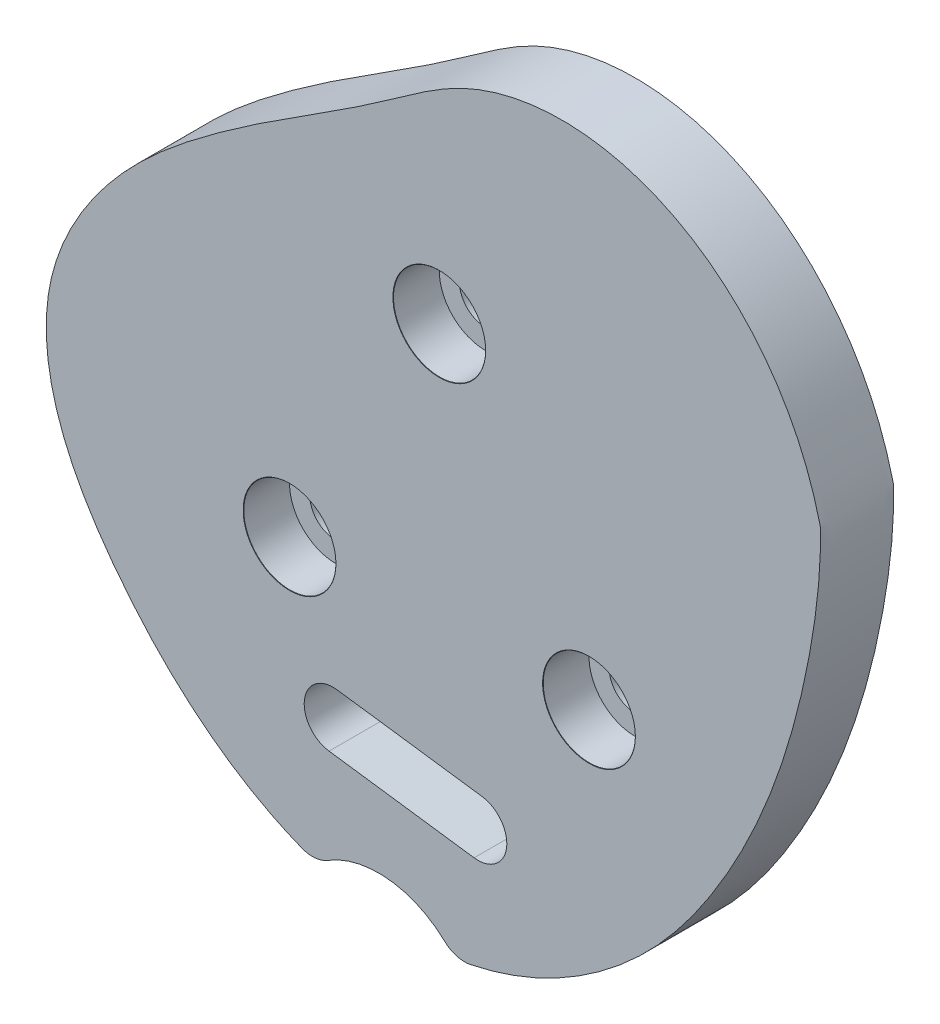
SolidWorks part; units mm, degrees
ref_plane "Front Plane" through (0, 0, 0) normal (0, 0, 1) x (1, 0, 0)
ref_plane "Top Plane" through (0, 0, 0) normal (0, 1, 0) x (1, 0, 0)
ref_plane "Right Plane" through (0, 0, 0) normal (1, 0, 0) x (0, 0, -1)
curve "Curve1"
sketch "Sketch1" plane through (0, 0, 0) normal (0, 0, 1) x (1, 0, 0)
  spline S0 degree 3 poles (20.4719, -0.3582) (20.4906, 0.0056) (20.3791, 0.3547) (20.2968, 0.7085) (20.2014, 1.0583) (20.1045, 1.4055) (20.003, 1.7496) (19.8979, 2.091) (19.7889, 2.4294) (19.6761, 2.7649) (19.5596, 3.0976) (19.4394, 3.4274) (19.3156, 3.7542) (19.1882, 4.0783) (19.0573, 4.3994) (18.9228, 4.7177) (18.7848, 5.0331) (18.6433, 5.3456) (18.4984, 5.6553) (18.3501, 5.962) (18.1985, 6.266) (18.0434, 6.567) (17.8851, 6.8652) (17.7235, 7.1605) (17.5586, 7.4529) (17.3904, 7.7425) (17.219, 8.0291) (17.0444, 8.3129) (16.8666, 8.5937) (16.6856, 8.8717) (16.5014, 9.1467) (16.3141, 9.4188) (16.1237, 9.6879) (15.9302, 9.9541) (15.7336, 10.2173) (15.5338, 10.4776) (15.3311, 10.7348) (15.1252, 10.989) (14.9164, 11.2402) (14.7045, 11.4883) (14.4895, 11.7333) (14.2716, 11.9752) (14.0507, 12.214) (13.8268, 12.4496) (13.5999, 12.6821) (13.3701, 12.9113) (13.1374, 13.1373) (12.9017, 13.3601) (12.6631, 13.5795) (12.4217, 13.7956) (12.1773, 14.0084) (11.9301, 14.2177) (11.68, 14.4236) (11.4271, 14.626) (11.1713, 14.8249) (10.9128, 15.0202) (10.6515, 15.212) (10.3875, 15.4001) (10.1207, 15.5845) (9.8512, 15.7652) (9.579, 15.9422) (9.3041, 16.1153) (9.0266, 16.2845) (8.7465, 16.4499) (8.4638, 16.6112) (8.1785, 16.7686) (7.8907, 16.9219) (7.6005, 17.0711) (7.3077, 17.2161) (7.0126, 17.357) (6.715, 17.4935) (6.4152, 17.6257) (6.113, 17.7536) (5.8085, 17.877) (5.5018, 17.996) (5.193, 18.1104) (4.882, 18.2202) (4.5689, 18.3254) (4.2539, 18.4259) (3.9368, 18.5217) (3.6178, 18.6126) (3.297, 18.6987) (2.9743, 18.7798) (2.6499, 18.856) (2.3239, 18.9272) (1.9962, 18.9933) (1.6669, 19.0543) (1.3362, 19.11) (1.0041, 19.1606) (0.6706, 19.2059) (0.3358, 19.2458) (-0.0001, 19.2804) (-0.3372, 19.3095) (-0.6752, 19.3332) (-1.0143, 19.3513) (-1.3542, 19.3639) (-1.6948, 19.3709) (-2.0362, 19.3722) (-2.3782, 19.3678) (-2.7207, 19.3577) (-3.0636, 19.3418) (-3.4068, 19.3201) (-3.7502, 19.2926) (-4.0938, 19.2592) (-4.4374, 19.2198) (-4.7809, 19.1746) (-5.1242, 19.1233) (-5.4672, 19.0661) (-5.8099, 19.0029) (-6.152, 18.9336) (-6.4935, 18.8583) (-6.8343, 18.7768) (-7.1743, 18.6893) (-7.5133, 18.5957) (-7.8512, 18.496) (-8.1879, 18.3901) (-8.5233, 18.2781) (-8.8573, 18.16) (-9.1898, 18.0358) (-9.5206, 17.9054) (-9.8496, 17.7689) (-10.1766, 17.6262) (-10.5017, 17.4775) (-10.8245, 17.3227) (-11.1451, 17.1617) (-11.4632, 16.9947) (-11.7791, 16.822) (-12.0927, 16.6439) (-12.4044, 16.4609) (-12.7144, 16.2733) (-13.0229, 16.0815) (-13.3301, 15.8857) (-13.6364, 15.6864) (-13.9422, 15.4837) (-14.2476, 15.278) (-14.5531, 15.0694) (-14.859, 14.8581) (-15.1658, 14.6444) (-15.4738, 14.4285) (-15.7835, 14.2103) (-16.0953, 13.99) (-16.4096, 13.7678) (-16.7269, 13.5435) (-17.0477, 13.3173) (-17.3725, 13.0891) (-17.7016, 12.8589) (-18.0357, 12.6265) (-18.3753, 12.3918) (-18.7207, 12.1548) (-19.0726, 11.9151) (-19.4314, 11.6726) (-19.7976, 11.4271) (-20.1718, 11.1782) (-20.5544, 10.9256) (-20.9459, 10.669) (-21.3468, 10.4079) (-21.7576, 10.142) (-22.1787, 9.8708) (-22.6107, 9.5937) (-23.0538, 9.3103) (-23.5087, 9.0201) (-23.9757, 8.7223) (-24.4552, 8.4163) (-24.9476, 8.1016) (-25.4532, 7.7775) (-25.9724, 7.443) (-26.5055, 7.0977) (-27.0528, 6.7405) (-27.6146, 6.3708) (-28.1911, 5.9877) (-28.7826, 5.5902) (-29.3891, 5.1775) (-30.011, 4.7487) (-30.6482, 4.3027) (-31.3009, 3.8387) (-31.9692, 3.3555) (-32.6531, 2.8522) (-33.3524, 2.3277) (-34.0663, 1.7816) (-34.7922, 1.212) (-35.5264, 0.6179) (-36.2656, -0.0015) (-37.006, -0.6467) (-37.7441, -1.3181) (-38.4762, -2.0158) (-39.1988, -2.7397) (-39.9081, -3.4895) (-40.6005, -4.2646) (-41.2726, -5.0643) (-41.9207, -5.8876) (-42.5414, -6.7333) (-43.1312, -7.6) (-43.6867, -8.4861) (-44.2047, -9.3896) (-44.6819, -10.3087) (-45.1152, -11.2411) (-45.5015, -12.1842) (-45.838, -13.1356) (-46.1218, -14.0922) (-46.3502, -15.0514) (-46.5207, -16.0105) (-46.6353, -16.9668) (-46.6959, -17.9187) (-46.7048, -18.8646) (-46.6641, -19.8031) (-46.576, -20.7331) (-46.4429, -21.6534) (-46.2667, -22.5631) (-46.0499, -23.4614) (-45.7945, -24.3476) (-45.5028, -25.2212) (-45.1769, -26.0818) (-44.8189, -26.9291) (-44.431, -27.763) (-44.0152, -28.5834) (-43.5736, -29.3905) (-43.1082, -30.1845) (-42.6208, -30.9657) (-42.1134, -31.7347) (-41.5877, -32.4919) (-41.0455, -33.2381) (-40.4886, -33.9741) (-39.9184, -34.7007) (-39.3348, -35.4173) (-38.7375, -36.1234) (-38.1264, -36.8183) (-37.5012, -37.5012) (-36.8618, -38.1715) (-36.2081, -38.8285) (-35.5401, -39.4713) (-34.8578, -40.0993) (-34.1611, -40.7116) (-33.4502, -41.3075) (-32.725, -41.8861) (-31.9858, -42.4467) (-31.2328, -42.9883) (-30.4661, -43.5102) (-29.686, -44.0114) (-28.8928, -44.4912) (-28.0869, -44.9487) (-27.2687, -45.383) (-26.4385, -45.7933) (-25.5969, -46.1786) (-24.7444, -46.5382) (-23.8816, -46.8712) (-23.009, -47.1767) (-22.1274, -47.454) (-21.2375, -47.7021) (-20.34, -47.9203) (-19.4357, -48.1077) (-18.5254, -48.2636) (-17.6101, -48.3873) (-16.6907, -48.4779) (-15.7681, -48.5348) (-14.8434, -48.5572) (-13.9176, -48.5444) (-12.9919, -48.4959) (-12.0676, -48.4109) (-11.1461, -48.29) (-10.2287, -48.1341) (-9.3169, -47.9441) (-8.412, -47.7209) (-7.5154, -47.4656) (-6.6283, -47.1791) (-5.7518, -46.8626) (-4.887, -46.5172) (-4.035, -46.144) (-3.1968, -45.7443) (-2.3733, -45.3192) (-1.5652, -44.87) (-0.7734, -44.398) (0.0014, -43.9045) (0.7587, -43.3908) (1.4978, -42.8582) (2.2183, -42.3081) (2.9197, -41.7419) (3.6018, -41.1608) (4.2642, -40.5664) (4.9068, -39.9599) (5.5294, -39.3427) (6.132, -38.7162) (6.7146, -38.0817) (7.2773, -37.4407) (7.8203, -36.7944) (8.3437, -36.1442) (8.8479, -35.4914) (9.3333, -34.8372) (9.8003, -34.183) (10.2494, -33.5299) (10.6811, -32.8793) (11.0962, -32.2321) (11.4952, -31.5897) (11.8791, -30.953) (12.2485, -30.3226) (12.6037, -29.6986) (12.9452, -29.0811) (13.2733, -28.4704) (13.5887, -27.8663) (13.8917, -27.2691) (14.1827, -26.6788) (14.4623, -26.0953) (14.7307, -25.5188) (14.9884, -24.9492) (15.2358, -24.3866) (15.4733, -23.8309) (15.7014, -23.2821) (15.9202, -22.7402) (16.1303, -22.2051) (16.332, -21.6768) (16.5257, -21.1552) (16.7115, -20.6403) (16.89, -20.1319) (17.0614, -19.63) (17.2261, -19.1344) (17.3842, -18.6451) (17.5361, -18.1619) (17.6822, -17.6848) (17.8225, -17.2135) (17.9574, -16.748) (18.0872, -16.2881) (18.2121, -15.8337) (18.3322, -15.3847) (18.4478, -14.9408) (18.5591, -14.5019) (18.6662, -14.0679) (18.7694, -13.6386) (18.8688, -13.2138) (18.9646, -12.7934) (19.0568, -12.3772) (19.1457, -11.9651) (19.2313, -11.5568) (19.3138, -11.1522) (19.3933, -10.7511) (19.4697, -10.3534) (19.5433, -9.959) (19.6141, -9.5675) (19.6821, -9.1789) (19.7474, -8.7931) (19.8101, -8.4098) (19.87, -8.0288) (19.9274, -7.6502) (19.9821, -7.2736) (20.0342, -6.899) (20.0836, -6.5262) (20.1304, -6.1551) (20.1746, -5.7855) (20.216, -5.4173) (20.2547, -5.0505) (20.2905, -4.6848) (20.3236, -4.3203) (20.3537, -3.9567) (20.3809, -3.594) (20.4049, -3.2321) (20.4259, -2.8709) (20.4437, -2.5104) (20.4581, -2.1504) (20.4692, -1.791) (20.4769, -1.432) (20.4803, -1.0735) (20.4824, -0.7151) (20.4719, -0.3582) (20.4906, 0.0056) (20.3791, 0.3547) knots -0.005175 -0.003449 -0.001724 0 0.001764 0.003519 0.005266 0.007004 0.008734 0.010456 0.01217 0.013877 0.015576 0.017268 0.018953 0.020632 0.022304 0.02397 0.02563 0.027283 0.028932 0.030575 0.032212 0.033845 0.035472 0.037095 0.038714 0.040328 0.041938 0.043545 0.045147 0.046746 0.048342 0.049935 0.051524 0.053111 0.054695 0.056276 0.057855 0.059432 0.061007 0.06258 0.064152 0.065721 0.06729 0.068857 0.070423 0.071988 0.073552 0.075115 0.076678 0.07824 0.079802 0.081364 0.082926 0.084488 0.08605 0.087612 0.089174 0.090737 0.092301 0.093865 0.095431 0.096997 0.098564 0.100132 0.101701 0.103272 0.104844 0.106418 0.107993 0.109569 0.111148 0.112728 0.11431 0.115894 0.117479 0.119067 0.120657 0.12225 0.123844 0.125441 0.12704 0.128642 0.130246 0.131852 0.133461 0.135073 0.136687 0.138304 0.139924 0.141547 0.143172 0.1448 0.146431 0.148065 0.149702 0.151342 0.152985 0.154631 0.156279 0.157931 0.159586 0.161244 0.162905 0.16457 0.166237 0.167907 0.169581 0.171258 0.172937 0.17462 0.176307 0.177996 0.179688 0.181384 0.183082 0.184784 0.186489 0.188197 0.189908 0.191622 0.19334 0.19506 0.196783 0.19851 0.200239 0.201971 0.203707 0.205446 0.207188 0.208935 0.210686 0.212442 0.214204 0.215972 0.217748 0.219531 0.221323 0.223125 0.224939 0.226765 0.228604 0.23046 0.232333 0.234225 0.236138 0.238074 0.240035 0.242024 0.244043 0.246095 0.248182 0.250307 0.252473 0.254682 0.256938 0.259244 0.261602 0.264016 0.26649 0.269025 0.271625 0.274295 0.277036 0.279852 0.282747 0.285724 0.288785 0.291935 0.295176 0.298513 0.301947 0.305484 0.309124 0.312873 0.316734 0.320709 0.324801 0.329015 0.333352 0.337803 0.34236 0.347013 0.351751 0.356565 0.361444 0.366378 0.371357 0.376371 0.38141 0.386464 0.391524 0.39658 0.401624 0.406647 0.411641 0.416599 0.421513 0.426378 0.431188 0.43594 0.440632 0.445271 0.449865 0.454421 0.458946 0.463447 0.467927 0.472391 0.476844 0.481289 0.485727 0.490163 0.494596 0.499029 0.503463 0.507898 0.512334 0.516773 0.521215 0.525659 0.530106 0.534555 0.539008 0.543464 0.547923 0.552384 0.556848 0.561315 0.565783 0.570252 0.574723 0.579195 0.583667 0.588139 0.592612 0.597084 0.601555 0.606025 0.610494 0.614962 0.619428 0.623892 0.628354 0.632814 0.637273 0.641729 0.646184 0.650638 0.65509 0.659542 0.663994 0.668446 0.672899 0.677354 0.681812 0.686275 0.690742 0.695217 0.699697 0.704183 0.708673 0.713166 0.717661 0.722155 0.726648 0.731137 0.735622 0.740099 0.744568 0.749025 0.75347 0.757899 0.762311 0.766703 0.771074 0.775421 0.779741 0.784033 0.788293 0.792521 0.796712 0.800866 0.804979 0.809049 0.813074 0.817052 0.82098 0.824856 0.828677 0.832443 0.83615 0.839797 0.843382 0.846904 0.850365 0.853767 0.857109 0.860394 0.863623 0.866796 0.869914 0.87298 0.875994 0.878957 0.88187 0.884735 0.887552 0.890324 0.89305 0.895732 0.898371 0.900968 0.903525 0.906043 0.908522 0.910963 0.913369 0.915739 0.918076 0.920379 0.922651 0.924892 0.927103 0.929285 0.93144 0.933569 0.935672 0.93775 0.939805 0.941838 0.943849 0.94584 0.94781 0.949763 0.951697 0.953615 0.955517 0.957403 0.959276 0.961134 0.962981 0.964815 0.966638 0.968451 0.970255 0.972049 0.973835 0.975613 0.977385 0.979149 0.980908 0.982662 0.98441 0.986154 0.987894 0.989631 0.991365 0.993096 0.994825 0.996551 0.998276 1 1.001764 1.003519 1.005266 only from (20.4693, 0) to (20.4693, 0) construction
  spline S1 degree 3 poles (20.4719, -0.3582) (20.4906, 0.0056) (20.3791, 0.3547) (20.2968, 0.7085) (20.2014, 1.0583) (20.1045, 1.4055) (20.003, 1.7496) (19.8979, 2.091) (19.7889, 2.4294) (19.6761, 2.7649) (19.5596, 3.0976) (19.4394, 3.4274) (19.3156, 3.7542) (19.1882, 4.0783) (19.0573, 4.3994) (18.9228, 4.7177) (18.7848, 5.0331) (18.6433, 5.3456) (18.4984, 5.6553) (18.3501, 5.962) (18.1985, 6.266) (18.0434, 6.567) (17.8851, 6.8652) (17.7235, 7.1605) (17.5586, 7.4529) (17.3904, 7.7425) (17.219, 8.0291) (17.0444, 8.3129) (16.8666, 8.5937) (16.6856, 8.8717) (16.5014, 9.1467) (16.3141, 9.4188) (16.1237, 9.6879) (15.9302, 9.9541) (15.7336, 10.2173) (15.5338, 10.4776) (15.3311, 10.7348) (15.1252, 10.989) (14.9164, 11.2402) (14.7045, 11.4883) (14.4895, 11.7333) (14.2716, 11.9752) (14.0507, 12.214) (13.8268, 12.4496) (13.5999, 12.6821) (13.3701, 12.9113) (13.1374, 13.1373) (12.9017, 13.3601) (12.6631, 13.5795) (12.4217, 13.7956) (12.1773, 14.0084) (11.9301, 14.2177) (11.68, 14.4236) (11.4271, 14.626) (11.1713, 14.8249) (10.9128, 15.0202) (10.6515, 15.212) (10.3875, 15.4001) (10.1207, 15.5845) (9.8512, 15.7652) (9.579, 15.9422) (9.3041, 16.1153) (9.0266, 16.2845) (8.7465, 16.4499) (8.4638, 16.6112) (8.1785, 16.7686) (7.8907, 16.9219) (7.6005, 17.0711) (7.3077, 17.2161) (7.0126, 17.357) (6.715, 17.4935) (6.4152, 17.6257) (6.113, 17.7536) (5.8085, 17.877) (5.5018, 17.996) (5.193, 18.1104) (4.882, 18.2202) (4.5689, 18.3254) (4.2539, 18.4259) (3.9368, 18.5217) (3.6178, 18.6126) (3.297, 18.6987) (2.9743, 18.7798) (2.6499, 18.856) (2.3239, 18.9272) (1.9962, 18.9933) (1.6669, 19.0543) (1.3362, 19.11) (1.0041, 19.1606) (0.6706, 19.2059) (0.3358, 19.2458) (-0.0001, 19.2804) (-0.3372, 19.3095) (-0.6752, 19.3332) (-1.0143, 19.3513) (-1.3542, 19.3639) (-1.6948, 19.3709) (-2.0362, 19.3722) (-2.3782, 19.3678) (-2.7207, 19.3577) (-3.0636, 19.3418) (-3.4068, 19.3201) (-3.7502, 19.2926) (-4.0938, 19.2592) (-4.4374, 19.2198) (-4.7809, 19.1746) (-5.1242, 19.1233) (-5.4672, 19.0661) (-5.8099, 19.0029) (-6.152, 18.9336) (-6.4935, 18.8583) (-6.8343, 18.7768) (-7.1743, 18.6893) (-7.5133, 18.5957) (-7.8512, 18.496) (-8.1879, 18.3901) (-8.5233, 18.2781) (-8.8573, 18.16) (-9.1898, 18.0358) (-9.5206, 17.9054) (-9.8496, 17.7689) (-10.1766, 17.6262) (-10.5017, 17.4775) (-10.8245, 17.3227) (-11.1451, 17.1617) (-11.4632, 16.9947) (-11.7791, 16.822) (-12.0927, 16.6439) (-12.4044, 16.4609) (-12.7144, 16.2733) (-13.0229, 16.0815) (-13.3301, 15.8857) (-13.6364, 15.6864) (-13.9422, 15.4837) (-14.2476, 15.278) (-14.5531, 15.0694) (-14.859, 14.8581) (-15.1658, 14.6444) (-15.4738, 14.4285) (-15.7835, 14.2103) (-16.0953, 13.99) (-16.4096, 13.7678) (-16.7269, 13.5435) (-17.0477, 13.3173) (-17.3725, 13.0891) (-17.7016, 12.8589) (-18.0357, 12.6265) (-18.3753, 12.3918) (-18.7207, 12.1548) (-19.0726, 11.9151) (-19.4314, 11.6726) (-19.7976, 11.4271) (-20.1718, 11.1782) (-20.5544, 10.9256) (-20.9459, 10.669) (-21.3468, 10.4079) (-21.7576, 10.142) (-22.1787, 9.8708) (-22.6107, 9.5937) (-23.0538, 9.3103) (-23.5087, 9.0201) (-23.9757, 8.7223) (-24.4552, 8.4163) (-24.9476, 8.1016) (-25.4532, 7.7775) (-25.9724, 7.443) (-26.5055, 7.0977) (-27.0528, 6.7405) (-27.6146, 6.3708) (-28.1911, 5.9877) (-28.7826, 5.5902) (-29.3891, 5.1775) (-30.011, 4.7487) (-30.6482, 4.3027) (-31.3009, 3.8387) (-31.9692, 3.3555) (-32.6531, 2.8522) (-33.3524, 2.3277) (-34.0663, 1.7816) (-34.7922, 1.212) (-35.5264, 0.6179) (-36.2656, -0.0015) (-37.006, -0.6467) (-37.7441, -1.3181) (-38.4762, -2.0158) (-39.1988, -2.7397) (-39.9081, -3.4895) (-40.6005, -4.2646) (-41.2726, -5.0643) (-41.9207, -5.8876) (-42.5414, -6.7333) (-43.1312, -7.6) (-43.6867, -8.4861) (-44.2047, -9.3896) (-44.6819, -10.3087) (-45.1152, -11.2411) (-45.5015, -12.1842) (-45.838, -13.1356) (-46.1218, -14.0922) (-46.3502, -15.0514) (-46.5207, -16.0105) (-46.6353, -16.9668) (-46.6959, -17.9187) (-46.7048, -18.8646) (-46.6641, -19.8031) (-46.576, -20.7331) (-46.4429, -21.6534) (-46.2667, -22.5631) (-46.0499, -23.4614) (-45.7945, -24.3476) (-45.5028, -25.2212) (-45.1769, -26.0818) (-44.8189, -26.9291) (-44.431, -27.763) (-44.0152, -28.5834) (-43.5736, -29.3905) (-43.1082, -30.1845) (-42.6208, -30.9657) (-42.1134, -31.7347) (-41.5877, -32.4919) (-41.0455, -33.2381) (-40.4886, -33.9741) (-39.9184, -34.7007) (-39.3348, -35.4173) (-38.7375, -36.1234) (-38.1264, -36.8183) (-37.5012, -37.5012) (-36.8618, -38.1715) (-36.2081, -38.8285) (-35.5401, -39.4713) (-34.8578, -40.0993) (-34.1611, -40.7116) (-33.4502, -41.3075) (-32.725, -41.8861) (-31.9858, -42.4467) (-31.2328, -42.9883) (-30.4661, -43.5102) (-29.686, -44.0114) (-28.8928, -44.4912) (-28.0869, -44.9487) (-27.2687, -45.383) (-26.4385, -45.7933) (-25.5969, -46.1786) (-24.7444, -46.5382) (-23.8816, -46.8712) (-23.009, -47.1767) (-22.1274, -47.454) (-21.2375, -47.7021) (-20.34, -47.9203) (-19.4357, -48.1077) (-18.5254, -48.2636) (-17.6101, -48.3873) (-16.6907, -48.4779) (-15.7681, -48.5348) (-14.8434, -48.5572) (-13.9176, -48.5444) (-12.9919, -48.4959) (-12.0676, -48.4109) (-11.1461, -48.29) (-10.2287, -48.1341) (-9.3169, -47.9441) (-8.412, -47.7209) (-7.5154, -47.4656) (-6.6283, -47.1791) (-5.7518, -46.8626) (-4.887, -46.5172) (-4.035, -46.144) (-3.1968, -45.7443) (-2.3733, -45.3192) (-1.5652, -44.87) (-0.7734, -44.398) (0.0014, -43.9045) (0.7587, -43.3908) (1.4978, -42.8582) (2.2183, -42.3081) (2.9197, -41.7419) (3.6018, -41.1608) (4.2642, -40.5664) (4.9068, -39.9599) (5.5294, -39.3427) (6.132, -38.7162) (6.7146, -38.0817) (7.2773, -37.4407) (7.8203, -36.7944) (8.3437, -36.1442) (8.8479, -35.4914) (9.3333, -34.8372) (9.8003, -34.183) (10.2494, -33.5299) (10.6811, -32.8793) (11.0962, -32.2321) (11.4952, -31.5897) (11.8791, -30.953) (12.2485, -30.3226) (12.6037, -29.6986) (12.9452, -29.0811) (13.2733, -28.4704) (13.5887, -27.8663) (13.8917, -27.2691) (14.1827, -26.6788) (14.4623, -26.0953) (14.7307, -25.5188) (14.9884, -24.9492) (15.2358, -24.3866) (15.4733, -23.8309) (15.7014, -23.2821) (15.9202, -22.7402) (16.1303, -22.2051) (16.332, -21.6768) (16.5257, -21.1552) (16.7115, -20.6403) (16.89, -20.1319) (17.0614, -19.63) (17.2261, -19.1344) (17.3842, -18.6451) (17.5361, -18.1619) (17.6822, -17.6848) (17.8225, -17.2135) (17.9574, -16.748) (18.0872, -16.2881) (18.2121, -15.8337) (18.3322, -15.3847) (18.4478, -14.9408) (18.5591, -14.5019) (18.6662, -14.0679) (18.7694, -13.6386) (18.8688, -13.2138) (18.9646, -12.7934) (19.0568, -12.3772) (19.1457, -11.9651) (19.2313, -11.5568) (19.3138, -11.1522) (19.3933, -10.7511) (19.4697, -10.3534) (19.5433, -9.959) (19.6141, -9.5675) (19.6821, -9.1789) (19.7474, -8.7931) (19.8101, -8.4098) (19.87, -8.0288) (19.9274, -7.6502) (19.9821, -7.2736) (20.0342, -6.899) (20.0836, -6.5262) (20.1304, -6.1551) (20.1746, -5.7855) (20.216, -5.4173) (20.2547, -5.0505) (20.2905, -4.6848) (20.3236, -4.3203) (20.3537, -3.9567) (20.3809, -3.594) (20.4049, -3.2321) (20.4259, -2.8709) (20.4437, -2.5104) (20.4581, -2.1504) (20.4692, -1.791) (20.4769, -1.432) (20.4803, -1.0735) (20.4824, -0.7151) (20.4719, -0.3582) (20.4906, 0.0056) (20.3791, 0.3547) knots -0.005175 -0.003449 -0.001724 0 0.001764 0.003519 0.005266 0.007004 0.008734 0.010456 0.01217 0.013877 0.015576 0.017268 0.018953 0.020632 0.022304 0.02397 0.02563 0.027283 0.028932 0.030575 0.032212 0.033845 0.035472 0.037095 0.038714 0.040328 0.041938 0.043545 0.045147 0.046746 0.048342 0.049935 0.051524 0.053111 0.054695 0.056276 0.057855 0.059432 0.061007 0.06258 0.064152 0.065721 0.06729 0.068857 0.070423 0.071988 0.073552 0.075115 0.076678 0.07824 0.079802 0.081364 0.082926 0.084488 0.08605 0.087612 0.089174 0.090737 0.092301 0.093865 0.095431 0.096997 0.098564 0.100132 0.101701 0.103272 0.104844 0.106418 0.107993 0.109569 0.111148 0.112728 0.11431 0.115894 0.117479 0.119067 0.120657 0.12225 0.123844 0.125441 0.12704 0.128642 0.130246 0.131852 0.133461 0.135073 0.136687 0.138304 0.139924 0.141547 0.143172 0.1448 0.146431 0.148065 0.149702 0.151342 0.152985 0.154631 0.156279 0.157931 0.159586 0.161244 0.162905 0.16457 0.166237 0.167907 0.169581 0.171258 0.172937 0.17462 0.176307 0.177996 0.179688 0.181384 0.183082 0.184784 0.186489 0.188197 0.189908 0.191622 0.19334 0.19506 0.196783 0.19851 0.200239 0.201971 0.203707 0.205446 0.207188 0.208935 0.210686 0.212442 0.214204 0.215972 0.217748 0.219531 0.221323 0.223125 0.224939 0.226765 0.228604 0.23046 0.232333 0.234225 0.236138 0.238074 0.240035 0.242024 0.244043 0.246095 0.248182 0.250307 0.252473 0.254682 0.256938 0.259244 0.261602 0.264016 0.26649 0.269025 0.271625 0.274295 0.277036 0.279852 0.282747 0.285724 0.288785 0.291935 0.295176 0.298513 0.301947 0.305484 0.309124 0.312873 0.316734 0.320709 0.324801 0.329015 0.333352 0.337803 0.34236 0.347013 0.351751 0.356565 0.361444 0.366378 0.371357 0.376371 0.38141 0.386464 0.391524 0.39658 0.401624 0.406647 0.411641 0.416599 0.421513 0.426378 0.431188 0.43594 0.440632 0.445271 0.449865 0.454421 0.458946 0.463447 0.467927 0.472391 0.476844 0.481289 0.485727 0.490163 0.494596 0.499029 0.503463 0.507898 0.512334 0.516773 0.521215 0.525659 0.530106 0.534555 0.539008 0.543464 0.547923 0.552384 0.556848 0.561315 0.565783 0.570252 0.574723 0.579195 0.583667 0.588139 0.592612 0.597084 0.601555 0.606025 0.610494 0.614962 0.619428 0.623892 0.628354 0.632814 0.637273 0.641729 0.646184 0.650638 0.65509 0.659542 0.663994 0.668446 0.672899 0.677354 0.681812 0.686275 0.690742 0.695217 0.699697 0.704183 0.708673 0.713166 0.717661 0.722155 0.726648 0.731137 0.735622 0.740099 0.744568 0.749025 0.75347 0.757899 0.762311 0.766703 0.771074 0.775421 0.779741 0.784033 0.788293 0.792521 0.796712 0.800866 0.804979 0.809049 0.813074 0.817052 0.82098 0.824856 0.828677 0.832443 0.83615 0.839797 0.843382 0.846904 0.850365 0.853767 0.857109 0.860394 0.863623 0.866796 0.869914 0.87298 0.875994 0.878957 0.88187 0.884735 0.887552 0.890324 0.89305 0.895732 0.898371 0.900968 0.903525 0.906043 0.908522 0.910963 0.913369 0.915739 0.918076 0.920379 0.922651 0.924892 0.927103 0.929285 0.93144 0.933569 0.935672 0.93775 0.939805 0.941838 0.943849 0.94584 0.94781 0.949763 0.951697 0.953615 0.955517 0.957403 0.959276 0.961134 0.962981 0.964815 0.966638 0.968451 0.970255 0.972049 0.973835 0.975613 0.977385 0.979149 0.980908 0.982662 0.98441 0.986154 0.987894 0.989631 0.991365 0.993096 0.994825 0.996551 0.998276 1 1.001764 1.003519 1.005266 only from (20.4693, 0) to (20.4693, 0)
extrude "Boss-Extrude1" add sketch "Sketch1" along normal mid plane 6.35
sketch "Sketch4" plane through (0, 0, 3.175) normal (0, 0, 1) x (1, 0, 0)
  line L0 (17.7659, -20.9602) -> (-1.4085, -53.5016) construction
  line L1 (-50.4616, -14.4148) -> (-15.5658, 21.7389) construction
  circle A0 centre (-12.5939, -16.2726) radius 28.5365 construction
  spline S0 degree 3 poles (20.4719, -0.3582) (20.4906, 0.0056) (20.3791, 0.3547) (20.2968, 0.7085) (20.2014, 1.0583) (20.1045, 1.4055) (20.003, 1.7496) (19.8979, 2.091) (19.7889, 2.4294) (19.6761, 2.7649) (19.5596, 3.0976) (19.4394, 3.4274) (19.3156, 3.7542) (19.1882, 4.0783) (19.0573, 4.3994) (18.9228, 4.7177) (18.7848, 5.0331) (18.6433, 5.3456) (18.4984, 5.6553) (18.3501, 5.962) (18.1985, 6.266) (18.0434, 6.567) (17.8851, 6.8652) (17.7235, 7.1605) (17.5586, 7.4529) (17.3904, 7.7425) (17.219, 8.0291) (17.0444, 8.3129) (16.8666, 8.5937) (16.6856, 8.8717) (16.5014, 9.1467) (16.3141, 9.4188) (16.1237, 9.6879) (15.9302, 9.9541) (15.7336, 10.2173) (15.5338, 10.4776) (15.3311, 10.7348) (15.1252, 10.989) (14.9164, 11.2402) (14.7045, 11.4883) (14.4895, 11.7333) (14.2716, 11.9752) (14.0507, 12.214) (13.8268, 12.4496) (13.5999, 12.6821) (13.3701, 12.9113) (13.1374, 13.1373) (12.9017, 13.3601) (12.6631, 13.5795) (12.4217, 13.7956) (12.1773, 14.0084) (11.9301, 14.2177) (11.68, 14.4236) (11.4271, 14.626) (11.1713, 14.8249) (10.9128, 15.0202) (10.6515, 15.212) (10.3875, 15.4001) (10.1207, 15.5845) (9.8512, 15.7652) (9.579, 15.9422) (9.3041, 16.1153) (9.0266, 16.2845) (8.7465, 16.4499) (8.4638, 16.6112) (8.1785, 16.7686) (7.8907, 16.9219) (7.6005, 17.0711) (7.3077, 17.2161) (7.0126, 17.357) (6.715, 17.4935) (6.4152, 17.6257) (6.113, 17.7536) (5.8085, 17.877) (5.5018, 17.996) (5.193, 18.1104) (4.882, 18.2202) (4.5689, 18.3254) (4.2539, 18.4259) (3.9368, 18.5217) (3.6178, 18.6126) (3.297, 18.6987) (2.9743, 18.7798) (2.6499, 18.856) (2.3239, 18.9272) (1.9962, 18.9933) (1.6669, 19.0543) (1.3362, 19.11) (1.0041, 19.1606) (0.6706, 19.2059) (0.3358, 19.2458) (-0.0001, 19.2804) (-0.3372, 19.3095) (-0.6752, 19.3332) (-1.0143, 19.3513) (-1.3542, 19.3639) (-1.6948, 19.3709) (-2.0362, 19.3722) (-2.3782, 19.3678) (-2.7207, 19.3577) (-3.0636, 19.3418) (-3.4068, 19.3201) (-3.7502, 19.2926) (-4.0938, 19.2592) (-4.4374, 19.2198) (-4.7809, 19.1746) (-5.1242, 19.1233) (-5.4672, 19.0661) (-5.8099, 19.0029) (-6.152, 18.9336) (-6.4935, 18.8583) (-6.8343, 18.7768) (-7.1743, 18.6893) (-7.5133, 18.5957) (-7.8512, 18.496) (-8.1879, 18.3901) (-8.5233, 18.2781) (-8.8573, 18.16) (-9.1898, 18.0358) (-9.5206, 17.9054) (-9.8496, 17.7689) (-10.1766, 17.6262) (-10.5017, 17.4775) (-10.8245, 17.3227) (-11.1451, 17.1617) (-11.4632, 16.9947) (-11.7791, 16.822) (-12.0927, 16.6439) (-12.4044, 16.4609) (-12.7144, 16.2733) (-13.0229, 16.0815) (-13.3301, 15.8857) (-13.6364, 15.6864) (-13.9422, 15.4837) (-14.2476, 15.278) (-14.5531, 15.0694) (-14.859, 14.8581) (-15.1658, 14.6444) (-15.4738, 14.4285) (-15.7835, 14.2103) (-16.0953, 13.99) (-16.4096, 13.7678) (-16.7269, 13.5435) (-17.0477, 13.3173) (-17.3725, 13.0891) (-17.7016, 12.8589) (-18.0357, 12.6265) (-18.3753, 12.3918) (-18.7207, 12.1548) (-19.0726, 11.9151) (-19.4314, 11.6726) (-19.7976, 11.4271) (-20.1718, 11.1782) (-20.5544, 10.9256) (-20.9459, 10.669) (-21.3468, 10.4079) (-21.7576, 10.142) (-22.1787, 9.8708) (-22.6107, 9.5937) (-23.0538, 9.3103) (-23.5087, 9.0201) (-23.9757, 8.7223) (-24.4552, 8.4163) (-24.9476, 8.1016) (-25.4532, 7.7775) (-25.9724, 7.443) (-26.5055, 7.0977) (-27.0528, 6.7405) (-27.6146, 6.3708) (-28.1911, 5.9877) (-28.7826, 5.5902) (-29.3891, 5.1775) (-30.011, 4.7487) (-30.6482, 4.3027) (-31.3009, 3.8387) (-31.9692, 3.3555) (-32.6531, 2.8522) (-33.3524, 2.3277) (-34.0663, 1.7816) (-34.7922, 1.212) (-35.5264, 0.6179) (-36.2656, -0.0015) (-37.006, -0.6467) (-37.7441, -1.3181) (-38.4762, -2.0158) (-39.1988, -2.7397) (-39.9081, -3.4895) (-40.6005, -4.2646) (-41.2726, -5.0643) (-41.9207, -5.8876) (-42.5414, -6.7333) (-43.1312, -7.6) (-43.6867, -8.4861) (-44.2047, -9.3896) (-44.6819, -10.3087) (-45.1152, -11.2411) (-45.5015, -12.1842) (-45.838, -13.1356) (-46.1218, -14.0922) (-46.3502, -15.0514) (-46.5207, -16.0105) (-46.6353, -16.9668) (-46.6959, -17.9187) (-46.7048, -18.8646) (-46.6641, -19.8031) (-46.576, -20.7331) (-46.4429, -21.6534) (-46.2667, -22.5631) (-46.0499, -23.4614) (-45.7945, -24.3476) (-45.5028, -25.2212) (-45.1769, -26.0818) (-44.8189, -26.9291) (-44.431, -27.763) (-44.0152, -28.5834) (-43.5736, -29.3905) (-43.1082, -30.1845) (-42.6208, -30.9657) (-42.1134, -31.7347) (-41.5877, -32.4919) (-41.0455, -33.2381) (-40.4886, -33.9741) (-39.9184, -34.7007) (-39.3348, -35.4173) (-38.7375, -36.1234) (-38.1264, -36.8183) (-37.5012, -37.5012) (-36.8618, -38.1715) (-36.2081, -38.8285) (-35.5401, -39.4713) (-34.8578, -40.0993) (-34.1611, -40.7116) (-33.4502, -41.3075) (-32.725, -41.8861) (-31.9858, -42.4467) (-31.2328, -42.9883) (-30.4661, -43.5102) (-29.686, -44.0114) (-28.8928, -44.4912) (-28.0869, -44.9487) (-27.2687, -45.383) (-26.4385, -45.7933) (-25.5969, -46.1786) (-24.7444, -46.5382) (-23.8816, -46.8712) (-23.009, -47.1767) (-22.1274, -47.454) (-21.2375, -47.7021) (-20.34, -47.9203) (-19.4357, -48.1077) (-18.5254, -48.2636) (-17.6101, -48.3873) (-16.6907, -48.4779) (-15.7681, -48.5348) (-14.8434, -48.5572) (-13.9176, -48.5444) (-12.9919, -48.4959) (-12.0676, -48.4109) (-11.1461, -48.29) (-10.2287, -48.1341) (-9.3169, -47.9441) (-8.412, -47.7209) (-7.5154, -47.4656) (-6.6283, -47.1791) (-5.7518, -46.8626) (-4.887, -46.5172) (-4.035, -46.144) (-3.1968, -45.7443) (-2.3733, -45.3192) (-1.5652, -44.87) (-0.7734, -44.398) (0.0014, -43.9045) (0.7587, -43.3908) (1.4978, -42.8582) (2.2183, -42.3081) (2.9197, -41.7419) (3.6018, -41.1608) (4.2642, -40.5664) (4.9068, -39.9599) (5.5294, -39.3427) (6.132, -38.7162) (6.7146, -38.0817) (7.2773, -37.4407) (7.8203, -36.7944) (8.3437, -36.1442) (8.8479, -35.4914) (9.3333, -34.8372) (9.8003, -34.183) (10.2494, -33.5299) (10.6811, -32.8793) (11.0962, -32.2321) (11.4952, -31.5897) (11.8791, -30.953) (12.2485, -30.3226) (12.6037, -29.6986) (12.9452, -29.0811) (13.2733, -28.4704) (13.5887, -27.8663) (13.8917, -27.2691) (14.1827, -26.6788) (14.4623, -26.0953) (14.7307, -25.5188) (14.9884, -24.9492) (15.2358, -24.3866) (15.4733, -23.8309) (15.7014, -23.2821) (15.9202, -22.7402) (16.1303, -22.2051) (16.332, -21.6768) (16.5257, -21.1552) (16.7115, -20.6403) (16.89, -20.1319) (17.0614, -19.63) (17.2261, -19.1344) (17.3842, -18.6451) (17.5361, -18.1619) (17.6822, -17.6848) (17.8225, -17.2135) (17.9574, -16.748) (18.0872, -16.2881) (18.2121, -15.8337) (18.3322, -15.3847) (18.4478, -14.9408) (18.5591, -14.5019) (18.6662, -14.0679) (18.7694, -13.6386) (18.8688, -13.2138) (18.9646, -12.7934) (19.0568, -12.3772) (19.1457, -11.9651) (19.2313, -11.5568) (19.3138, -11.1522) (19.3933, -10.7511) (19.4697, -10.3534) (19.5433, -9.959) (19.6141, -9.5675) (19.6821, -9.1789) (19.7474, -8.7931) (19.8101, -8.4098) (19.87, -8.0288) (19.9274, -7.6502) (19.9821, -7.2736) (20.0342, -6.899) (20.0836, -6.5262) (20.1304, -6.1551) (20.1746, -5.7855) (20.216, -5.4173) (20.2547, -5.0505) (20.2905, -4.6848) (20.3236, -4.3203) (20.3537, -3.9567) (20.3809, -3.594) (20.4049, -3.2321) (20.4259, -2.8709) (20.4437, -2.5104) (20.4581, -2.1504) (20.4692, -1.791) (20.4769, -1.432) (20.4803, -1.0735) (20.4824, -0.7151) (20.4719, -0.3582) (20.4906, 0.0056) (20.3791, 0.3547) knots -0.005175 -0.003449 -0.001724 0 0.001764 0.003519 0.005266 0.007004 0.008734 0.010456 0.01217 0.013877 0.015576 0.017268 0.018953 0.020632 0.022304 0.02397 0.02563 0.027283 0.028932 0.030575 0.032212 0.033845 0.035472 0.037095 0.038714 0.040328 0.041938 0.043545 0.045147 0.046746 0.048342 0.049935 0.051524 0.053111 0.054695 0.056276 0.057855 0.059432 0.061007 0.06258 0.064152 0.065721 0.06729 0.068857 0.070423 0.071988 0.073552 0.075115 0.076678 0.07824 0.079802 0.081364 0.082926 0.084488 0.08605 0.087612 0.089174 0.090737 0.092301 0.093865 0.095431 0.096997 0.098564 0.100132 0.101701 0.103272 0.104844 0.106418 0.107993 0.109569 0.111148 0.112728 0.11431 0.115894 0.117479 0.119067 0.120657 0.12225 0.123844 0.125441 0.12704 0.128642 0.130246 0.131852 0.133461 0.135073 0.136687 0.138304 0.139924 0.141547 0.143172 0.1448 0.146431 0.148065 0.149702 0.151342 0.152985 0.154631 0.156279 0.157931 0.159586 0.161244 0.162905 0.16457 0.166237 0.167907 0.169581 0.171258 0.172937 0.17462 0.176307 0.177996 0.179688 0.181384 0.183082 0.184784 0.186489 0.188197 0.189908 0.191622 0.19334 0.19506 0.196783 0.19851 0.200239 0.201971 0.203707 0.205446 0.207188 0.208935 0.210686 0.212442 0.214204 0.215972 0.217748 0.219531 0.221323 0.223125 0.224939 0.226765 0.228604 0.23046 0.232333 0.234225 0.236138 0.238074 0.240035 0.242024 0.244043 0.246095 0.248182 0.250307 0.252473 0.254682 0.256938 0.259244 0.261602 0.264016 0.26649 0.269025 0.271625 0.274295 0.277036 0.279852 0.282747 0.285724 0.288785 0.291935 0.295176 0.298513 0.301947 0.305484 0.309124 0.312873 0.316734 0.320709 0.324801 0.329015 0.333352 0.337803 0.34236 0.347013 0.351751 0.356565 0.361444 0.366378 0.371357 0.376371 0.38141 0.386464 0.391524 0.39658 0.401624 0.406647 0.411641 0.416599 0.421513 0.426378 0.431188 0.43594 0.440632 0.445271 0.449865 0.454421 0.458946 0.463447 0.467927 0.472391 0.476844 0.481289 0.485727 0.490163 0.494596 0.499029 0.503463 0.507898 0.512334 0.516773 0.521215 0.525659 0.530106 0.534555 0.539008 0.543464 0.547923 0.552384 0.556848 0.561315 0.565783 0.570252 0.574723 0.579195 0.583667 0.588139 0.592612 0.597084 0.601555 0.606025 0.610494 0.614962 0.619428 0.623892 0.628354 0.632814 0.637273 0.641729 0.646184 0.650638 0.65509 0.659542 0.663994 0.668446 0.672899 0.677354 0.681812 0.686275 0.690742 0.695217 0.699697 0.704183 0.708673 0.713166 0.717661 0.722155 0.726648 0.731137 0.735622 0.740099 0.744568 0.749025 0.75347 0.757899 0.762311 0.766703 0.771074 0.775421 0.779741 0.784033 0.788293 0.792521 0.796712 0.800866 0.804979 0.809049 0.813074 0.817052 0.82098 0.824856 0.828677 0.832443 0.83615 0.839797 0.843382 0.846904 0.850365 0.853767 0.857109 0.860394 0.863623 0.866796 0.869914 0.87298 0.875994 0.878957 0.88187 0.884735 0.887552 0.890324 0.89305 0.895732 0.898371 0.900968 0.903525 0.906043 0.908522 0.910963 0.913369 0.915739 0.918076 0.920379 0.922651 0.924892 0.927103 0.929285 0.93144 0.933569 0.935672 0.93775 0.939805 0.941838 0.943849 0.94584 0.94781 0.949763 0.951697 0.953615 0.955517 0.957403 0.959276 0.961134 0.962981 0.964815 0.966638 0.968451 0.970255 0.972049 0.973835 0.975613 0.977385 0.979149 0.980908 0.982662 0.98441 0.986154 0.987894 0.989631 0.991365 0.993096 0.994825 0.996551 0.998276 1 1.001764 1.003519 1.005266 only from (20.4693, 0) to (20.4693, 0) construction
  point P5 (-12.5939, -1.2726)
  point P6 (0.3965, -23.7726)
  point P11 (-25.5843, -23.7726)
  point P12 (-12.5939, -16.2726)
  dimension "D1" = 3
  dimension "D2" = 15
hole_wizard "CBORE for M4 SHCS1" positions "Sketch5" profile "Sketch7" counterbore size "M4" standard "ANSI Metric" end condition through all
sketch "Sketch5" plane through (0, 0, 3.175) normal (0, 0, 1) x (1, 0, 0)
  point P0 (-12.5939, -1.2726)
  point P3 (0.3965, -23.7726)
  point P6 (-25.5843, -23.7726)
sketch "Sketch7" plane through (-12.5939, -1.2726, 3.175) normal (1, 0, 0) x (0, -1, 0)
  line L0 (0, 0) -> (0, 6.35)
  line L1 (0, 6.35) -> (2.25, 6.35)
  line L3 (2.25, 6.35) -> (2.25, 4)
  line L4 (4, 4) -> (2.25, 4)
  line L5 (4, 4) -> (4, 0.025)
  line L6 (4, 0.025) -> (4.025, 0)
  line L7 (4.025, 0) -> (0, 0)
  line L8 (-4, 0.025) -> (-4.025, 0) construction
  line L11 (0, -6.35) -> (0, 107.95) construction
  dimension "Thru Hole Dia." = 4.5
  dimension "Thru Hole Depth" = 6.35
  dimension "C'Bore Dia." = 8
  dimension "C'Bore Depth" = 4
  dimension "Near C'Sink Dia." = 8.05
  dimension "Near C'Sink Angle" = 90
sketch "Sketch8" plane through (0, 0, 3.175) normal (0, 0, 1) x (1, 0, 0)
  line L0 (-21.8158, -35.6795) -> (-9.2335, -37.4044) construction
  line L3 (-21.4763, -33.2027) -> (-8.894, -34.9276)
  line L4 (-22.1554, -38.1564) -> (-9.573, -39.8813)
  line L5 (-15.5247, -36.542) -> (-17.1545, -48.4308) construction
  line L6 (-24.717, -48.7497) -> (-10.0918, -50.4122)
  arc A2 (-21.4763, -33.2027) -> (-22.1554, -38.1564) centre (-21.8158, -35.6795) ccw
  arc A3 (-9.573, -39.8813) -> (-8.894, -34.9276) centre (-9.2335, -37.4044) ccw
  arc A4 (-24.717, -48.7497) -> (-10.0918, -50.4122) centre (-17.8523, -53.5211) cw
  spline S1 degree 3 poles (20.4719, -0.3582) (20.4906, 0.0056) (20.3791, 0.3547) (20.2968, 0.7085) (20.2014, 1.0583) (20.1045, 1.4055) (20.003, 1.7496) (19.8979, 2.091) (19.7889, 2.4294) (19.6761, 2.7649) (19.5596, 3.0976) (19.4394, 3.4274) (19.3156, 3.7542) (19.1882, 4.0783) (19.0573, 4.3994) (18.9228, 4.7177) (18.7848, 5.0331) (18.6433, 5.3456) (18.4984, 5.6553) (18.3501, 5.962) (18.1985, 6.266) (18.0434, 6.567) (17.8851, 6.8652) (17.7235, 7.1605) (17.5586, 7.4529) (17.3904, 7.7425) (17.219, 8.0291) (17.0444, 8.3129) (16.8666, 8.5937) (16.6856, 8.8717) (16.5014, 9.1467) (16.3141, 9.4188) (16.1237, 9.6879) (15.9302, 9.9541) (15.7336, 10.2173) (15.5338, 10.4776) (15.3311, 10.7348) (15.1252, 10.989) (14.9164, 11.2402) (14.7045, 11.4883) (14.4895, 11.7333) (14.2716, 11.9752) (14.0507, 12.214) (13.8268, 12.4496) (13.5999, 12.6821) (13.3701, 12.9113) (13.1374, 13.1373) (12.9017, 13.3601) (12.6631, 13.5795) (12.4217, 13.7956) (12.1773, 14.0084) (11.9301, 14.2177) (11.68, 14.4236) (11.4271, 14.626) (11.1713, 14.8249) (10.9128, 15.0202) (10.6515, 15.212) (10.3875, 15.4001) (10.1207, 15.5845) (9.8512, 15.7652) (9.579, 15.9422) (9.3041, 16.1153) (9.0266, 16.2845) (8.7465, 16.4499) (8.4638, 16.6112) (8.1785, 16.7686) (7.8907, 16.9219) (7.6005, 17.0711) (7.3077, 17.2161) (7.0126, 17.357) (6.715, 17.4935) (6.4152, 17.6257) (6.113, 17.7536) (5.8085, 17.877) (5.5018, 17.996) (5.193, 18.1104) (4.882, 18.2202) (4.5689, 18.3254) (4.2539, 18.4259) (3.9368, 18.5217) (3.6178, 18.6126) (3.297, 18.6987) (2.9743, 18.7798) (2.6499, 18.856) (2.3239, 18.9272) (1.9962, 18.9933) (1.6669, 19.0543) (1.3362, 19.11) (1.0041, 19.1606) (0.6706, 19.2059) (0.3358, 19.2458) (-0.0001, 19.2804) (-0.3372, 19.3095) (-0.6752, 19.3332) (-1.0143, 19.3513) (-1.3542, 19.3639) (-1.6948, 19.3709) (-2.0362, 19.3722) (-2.3782, 19.3678) (-2.7207, 19.3577) (-3.0636, 19.3418) (-3.4068, 19.3201) (-3.7502, 19.2926) (-4.0938, 19.2592) (-4.4374, 19.2198) (-4.7809, 19.1746) (-5.1242, 19.1233) (-5.4672, 19.0661) (-5.8099, 19.0029) (-6.152, 18.9336) (-6.4935, 18.8583) (-6.8343, 18.7768) (-7.1743, 18.6893) (-7.5133, 18.5957) (-7.8512, 18.496) (-8.1879, 18.3901) (-8.5233, 18.2781) (-8.8573, 18.16) (-9.1898, 18.0358) (-9.5206, 17.9054) (-9.8496, 17.7689) (-10.1766, 17.6262) (-10.5017, 17.4775) (-10.8245, 17.3227) (-11.1451, 17.1617) (-11.4632, 16.9947) (-11.7791, 16.822) (-12.0927, 16.6439) (-12.4044, 16.4609) (-12.7144, 16.2733) (-13.0229, 16.0815) (-13.3301, 15.8857) (-13.6364, 15.6864) (-13.9422, 15.4837) (-14.2476, 15.278) (-14.5531, 15.0694) (-14.859, 14.8581) (-15.1658, 14.6444) (-15.4738, 14.4285) (-15.7835, 14.2103) (-16.0953, 13.99) (-16.4096, 13.7678) (-16.7269, 13.5435) (-17.0477, 13.3173) (-17.3725, 13.0891) (-17.7016, 12.8589) (-18.0357, 12.6265) (-18.3753, 12.3918) (-18.7207, 12.1548) (-19.0726, 11.9151) (-19.4314, 11.6726) (-19.7976, 11.4271) (-20.1718, 11.1782) (-20.5544, 10.9256) (-20.9459, 10.669) (-21.3468, 10.4079) (-21.7576, 10.142) (-22.1787, 9.8708) (-22.6107, 9.5937) (-23.0538, 9.3103) (-23.5087, 9.0201) (-23.9757, 8.7223) (-24.4552, 8.4163) (-24.9476, 8.1016) (-25.4532, 7.7775) (-25.9724, 7.443) (-26.5055, 7.0977) (-27.0528, 6.7405) (-27.6146, 6.3708) (-28.1911, 5.9877) (-28.7826, 5.5902) (-29.3891, 5.1775) (-30.011, 4.7487) (-30.6482, 4.3027) (-31.3009, 3.8387) (-31.9692, 3.3555) (-32.6531, 2.8522) (-33.3524, 2.3277) (-34.0663, 1.7816) (-34.7922, 1.212) (-35.5264, 0.6179) (-36.2656, -0.0015) (-37.006, -0.6467) (-37.7441, -1.3181) (-38.4762, -2.0158) (-39.1988, -2.7397) (-39.9081, -3.4895) (-40.6005, -4.2646) (-41.2726, -5.0643) (-41.9207, -5.8876) (-42.5414, -6.7333) (-43.1312, -7.6) (-43.6867, -8.4861) (-44.2047, -9.3896) (-44.6819, -10.3087) (-45.1152, -11.2411) (-45.5015, -12.1842) (-45.838, -13.1356) (-46.1218, -14.0922) (-46.3502, -15.0514) (-46.5207, -16.0105) (-46.6353, -16.9668) (-46.6959, -17.9187) (-46.7048, -18.8646) (-46.6641, -19.8031) (-46.576, -20.7331) (-46.4429, -21.6534) (-46.2667, -22.5631) (-46.0499, -23.4614) (-45.7945, -24.3476) (-45.5028, -25.2212) (-45.1769, -26.0818) (-44.8189, -26.9291) (-44.431, -27.763) (-44.0152, -28.5834) (-43.5736, -29.3905) (-43.1082, -30.1845) (-42.6208, -30.9657) (-42.1134, -31.7347) (-41.5877, -32.4919) (-41.0455, -33.2381) (-40.4886, -33.9741) (-39.9184, -34.7007) (-39.3348, -35.4173) (-38.7375, -36.1234) (-38.1264, -36.8183) (-37.5012, -37.5012) (-36.8618, -38.1715) (-36.2081, -38.8285) (-35.5401, -39.4713) (-34.8578, -40.0993) (-34.1611, -40.7116) (-33.4502, -41.3075) (-32.725, -41.8861) (-31.9858, -42.4467) (-31.2328, -42.9883) (-30.4661, -43.5102) (-29.686, -44.0114) (-28.8928, -44.4912) (-28.0869, -44.9487) (-27.2687, -45.383) (-26.4385, -45.7933) (-25.5969, -46.1786) (-24.7444, -46.5382) (-23.8816, -46.8712) (-23.009, -47.1767) (-22.1274, -47.454) (-21.2375, -47.7021) (-20.34, -47.9203) (-19.4357, -48.1077) (-18.5254, -48.2636) (-17.6101, -48.3873) (-16.6907, -48.4779) (-15.7681, -48.5348) (-14.8434, -48.5572) (-13.9176, -48.5444) (-12.9919, -48.4959) (-12.0676, -48.4109) (-11.1461, -48.29) (-10.2287, -48.1341) (-9.3169, -47.9441) (-8.412, -47.7209) (-7.5154, -47.4656) (-6.6283, -47.1791) (-5.7518, -46.8626) (-4.887, -46.5172) (-4.035, -46.144) (-3.1968, -45.7443) (-2.3733, -45.3192) (-1.5652, -44.87) (-0.7734, -44.398) (0.0014, -43.9045) (0.7587, -43.3908) (1.4978, -42.8582) (2.2183, -42.3081) (2.9197, -41.7419) (3.6018, -41.1608) (4.2642, -40.5664) (4.9068, -39.9599) (5.5294, -39.3427) (6.132, -38.7162) (6.7146, -38.0817) (7.2773, -37.4407) (7.8203, -36.7944) (8.3437, -36.1442) (8.8479, -35.4914) (9.3333, -34.8372) (9.8003, -34.183) (10.2494, -33.5299) (10.6811, -32.8793) (11.0962, -32.2321) (11.4952, -31.5897) (11.8791, -30.953) (12.2485, -30.3226) (12.6037, -29.6986) (12.9452, -29.0811) (13.2733, -28.4704) (13.5887, -27.8663) (13.8917, -27.2691) (14.1827, -26.6788) (14.4623, -26.0953) (14.7307, -25.5188) (14.9884, -24.9492) (15.2358, -24.3866) (15.4733, -23.8309) (15.7014, -23.2821) (15.9202, -22.7402) (16.1303, -22.2051) (16.332, -21.6768) (16.5257, -21.1552) (16.7115, -20.6403) (16.89, -20.1319) (17.0614, -19.63) (17.2261, -19.1344) (17.3842, -18.6451) (17.5361, -18.1619) (17.6822, -17.6848) (17.8225, -17.2135) (17.9574, -16.748) (18.0872, -16.2881) (18.2121, -15.8337) (18.3322, -15.3847) (18.4478, -14.9408) (18.5591, -14.5019) (18.6662, -14.0679) (18.7694, -13.6386) (18.8688, -13.2138) (18.9646, -12.7934) (19.0568, -12.3772) (19.1457, -11.9651) (19.2313, -11.5568) (19.3138, -11.1522) (19.3933, -10.7511) (19.4697, -10.3534) (19.5433, -9.959) (19.6141, -9.5675) (19.6821, -9.1789) (19.7474, -8.7931) (19.8101, -8.4098) (19.87, -8.0288) (19.9274, -7.6502) (19.9821, -7.2736) (20.0342, -6.899) (20.0836, -6.5262) (20.1304, -6.1551) (20.1746, -5.7855) (20.216, -5.4173) (20.2547, -5.0505) (20.2905, -4.6848) (20.3236, -4.3203) (20.3537, -3.9567) (20.3809, -3.594) (20.4049, -3.2321) (20.4259, -2.8709) (20.4437, -2.5104) (20.4581, -2.1504) (20.4692, -1.791) (20.4769, -1.432) (20.4803, -1.0735) (20.4824, -0.7151) (20.4719, -0.3582) (20.4906, 0.0056) (20.3791, 0.3547) knots -0.005175 -0.003449 -0.001724 0 0.001764 0.003519 0.005266 0.007004 0.008734 0.010456 0.01217 0.013877 0.015576 0.017268 0.018953 0.020632 0.022304 0.02397 0.02563 0.027283 0.028932 0.030575 0.032212 0.033845 0.035472 0.037095 0.038714 0.040328 0.041938 0.043545 0.045147 0.046746 0.048342 0.049935 0.051524 0.053111 0.054695 0.056276 0.057855 0.059432 0.061007 0.06258 0.064152 0.065721 0.06729 0.068857 0.070423 0.071988 0.073552 0.075115 0.076678 0.07824 0.079802 0.081364 0.082926 0.084488 0.08605 0.087612 0.089174 0.090737 0.092301 0.093865 0.095431 0.096997 0.098564 0.100132 0.101701 0.103272 0.104844 0.106418 0.107993 0.109569 0.111148 0.112728 0.11431 0.115894 0.117479 0.119067 0.120657 0.12225 0.123844 0.125441 0.12704 0.128642 0.130246 0.131852 0.133461 0.135073 0.136687 0.138304 0.139924 0.141547 0.143172 0.1448 0.146431 0.148065 0.149702 0.151342 0.152985 0.154631 0.156279 0.157931 0.159586 0.161244 0.162905 0.16457 0.166237 0.167907 0.169581 0.171258 0.172937 0.17462 0.176307 0.177996 0.179688 0.181384 0.183082 0.184784 0.186489 0.188197 0.189908 0.191622 0.19334 0.19506 0.196783 0.19851 0.200239 0.201971 0.203707 0.205446 0.207188 0.208935 0.210686 0.212442 0.214204 0.215972 0.217748 0.219531 0.221323 0.223125 0.224939 0.226765 0.228604 0.23046 0.232333 0.234225 0.236138 0.238074 0.240035 0.242024 0.244043 0.246095 0.248182 0.250307 0.252473 0.254682 0.256938 0.259244 0.261602 0.264016 0.26649 0.269025 0.271625 0.274295 0.277036 0.279852 0.282747 0.285724 0.288785 0.291935 0.295176 0.298513 0.301947 0.305484 0.309124 0.312873 0.316734 0.320709 0.324801 0.329015 0.333352 0.337803 0.34236 0.347013 0.351751 0.356565 0.361444 0.366378 0.371357 0.376371 0.38141 0.386464 0.391524 0.39658 0.401624 0.406647 0.411641 0.416599 0.421513 0.426378 0.431188 0.43594 0.440632 0.445271 0.449865 0.454421 0.458946 0.463447 0.467927 0.472391 0.476844 0.481289 0.485727 0.490163 0.494596 0.499029 0.503463 0.507898 0.512334 0.516773 0.521215 0.525659 0.530106 0.534555 0.539008 0.543464 0.547923 0.552384 0.556848 0.561315 0.565783 0.570252 0.574723 0.579195 0.583667 0.588139 0.592612 0.597084 0.601555 0.606025 0.610494 0.614962 0.619428 0.623892 0.628354 0.632814 0.637273 0.641729 0.646184 0.650638 0.65509 0.659542 0.663994 0.668446 0.672899 0.677354 0.681812 0.686275 0.690742 0.695217 0.699697 0.704183 0.708673 0.713166 0.717661 0.722155 0.726648 0.731137 0.735622 0.740099 0.744568 0.749025 0.75347 0.757899 0.762311 0.766703 0.771074 0.775421 0.779741 0.784033 0.788293 0.792521 0.796712 0.800866 0.804979 0.809049 0.813074 0.817052 0.82098 0.824856 0.828677 0.832443 0.83615 0.839797 0.843382 0.846904 0.850365 0.853767 0.857109 0.860394 0.863623 0.866796 0.869914 0.87298 0.875994 0.878957 0.88187 0.884735 0.887552 0.890324 0.89305 0.895732 0.898371 0.900968 0.903525 0.906043 0.908522 0.910963 0.913369 0.915739 0.918076 0.920379 0.922651 0.924892 0.927103 0.929285 0.93144 0.933569 0.935672 0.93775 0.939805 0.941838 0.943849 0.94584 0.94781 0.949763 0.951697 0.953615 0.955517 0.957403 0.959276 0.961134 0.962981 0.964815 0.966638 0.968451 0.970255 0.972049 0.973835 0.975613 0.977385 0.979149 0.980908 0.982662 0.98441 0.986154 0.987894 0.989631 0.991365 0.993096 0.994825 0.996551 0.998276 1 1.001764 1.003519 1.005266 only from (20.4693, 0) to (20.4693, 0) construction
  point P2 (-15.5247, -36.542)
  dimension "D1" = 12.7
  dimension "D2" = 5
  dimension "D3" = 12
extrude "Cut-Extrude1" cut sketch "Sketch8" against normal through all both and the other way through all
fillet "Fillet1" radius 2.5 2 edges at (-23.2103, -47.1038, 0) (-11.3158, -48.3091, 0)
